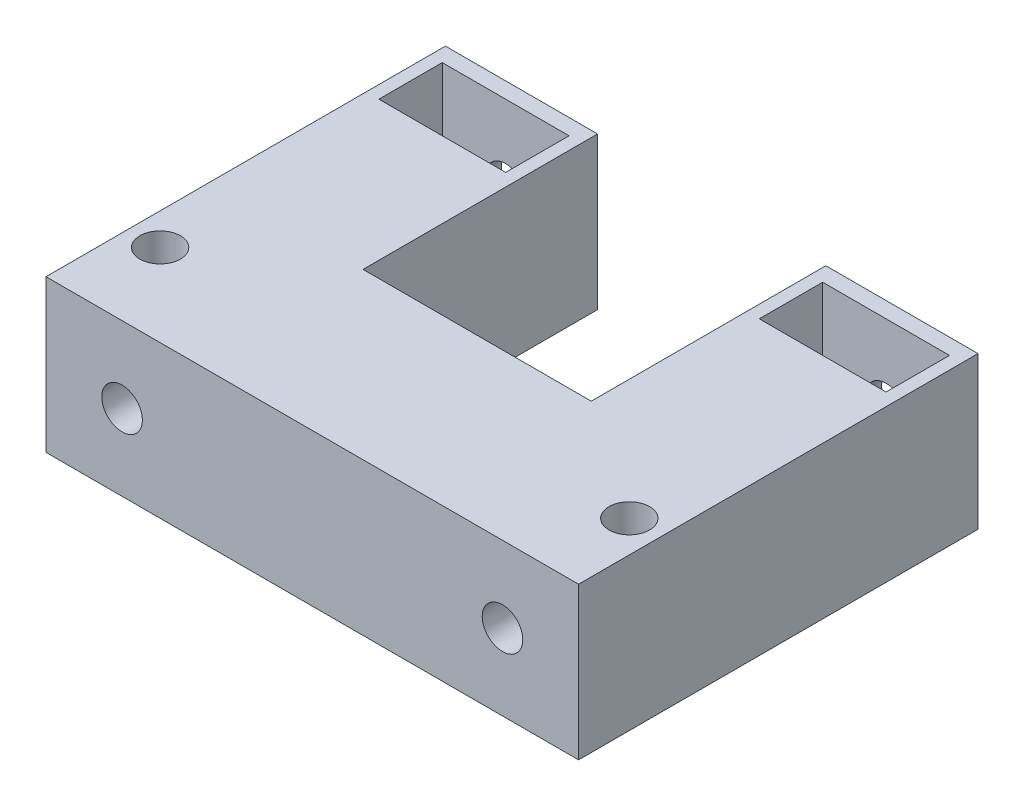
SolidWorks part; units mm, degrees
ref_plane "Alzado" through (0, 0, 0) normal (0, 0, 1) x (1, 0, 0)
ref_plane "Planta" through (0, 0, 0) normal (0, 1, 0) x (1, 0, 0)
ref_plane "Vista lateral" through (0, 0, 0) normal (1, 0, 0) x (0, 0, -1)
sketch "Croquis2" plane through (0, 0, 0) normal (0, 0, 1) x (1, 0, 0)
  line L0 (-5, -5) -> (-5, -6)
  line L1 (6, -6) -> (-6, -6)
  line L2 (6, -6) -> (6, 6)
  line L3 (6, 6) -> (-6, 6)
  line L4 (-6, -6) -> (-6, 6)
  line L7 (5, -5) -> (-5, -5)
  line L8 (5, -5) -> (5, 5)
  line L9 (5, 5) -> (-5, 5)
  line L10 (-5, -5) -> (-5, 5)
  line L14 (-5, 5) -> (-5, 6)
  line L15 (-5, 6) -> (-6, 6)
  line L16 (-6, 5) -> (-6, 6)
  line L17 (5, -5) -> (5, -6)
  line L18 (5, 5) -> (5, 6)
  point P0 (0, 0)
  point P6 (0, 0)
  dimension "D1" = 12
  dimension "D2" = 12
  dimension "D4" = 10
extrude "Saliente-Extruir1" add sketch "Croquis2" along normal blind 5 contours L10 L14 L3 L4 L1 L0 | L18 L8 L17 L1 L2 L3
sketch "Croquis3" plane through (0, 0, 0) normal (0, 0, -1) x (-1, 0, 0)
  line L0 (-6, -6) -> (-6, 6) construction
  line L1 (6, -6) -> (-6, -6)
  line L2 (6, -6) -> (6, 6)
  line L3 (6, 6) -> (-6, 6)
  line L4 (-6, -6) -> (-6, 6)
  line L5 (6, -6) -> (-6, 6) construction
  line L6 (6, 6) -> (-6, -6) construction
  point P0 (0, 0)
extrude "Saliente-Extruir2" add sketch "Croquis3" along normal blind 1.25
sketch "Croquis4" plane through (0, 0, 5) normal (0, 0, 1) x (1, 0, 0)
  line L1 (6, -6) -> (-6, -6)
  line L2 (6, -6) -> (6, 6)
  line L3 (6, 6) -> (-6, 6)
  line L4 (-6, -6) -> (-6, 6)
  line L5 (6, -6) -> (-6, 6) construction
  line L6 (6, 6) -> (-6, -6) construction
  point P0 (0, 0)
extrude "Saliente-Extruir3" add sketch "Croquis4" along normal blind 1.25
sketch "Croquis5" plane through (0, 0, 6.25) normal (0, 0, 1) x (1, 0, 0)
  circle A0 centre (0, 0) radius 1.6
extrude "Cortar-Extruir1" cut sketch "Croquis5" against normal blind 1.25
sketch "Croquis7" plane through (0, 0, 0) normal (0, 0, 1) x (1, 0, 0)
  line L1 (-6, -6) -> (6, -6)
  line L2 (-6, -6) -> (-6, 6)
  line L3 (-6, 6) -> (6, 6)
  line L4 (6, -6) -> (6, 6)
  line L5 (-6, -6) -> (6, 6) construction
  line L6 (-6, 6) -> (6, -6) construction
  circle A0 centre (0, 0) radius 1.6
sketch "Croquis9" plane through (0, 0, 0) normal (0, 0, 1) x (1, 0, 0)
  line L0 (-6, 6) -> (6, -6) construction
  circle A0 centre (0, 0) radius 1.6
extrude "Cortar-Extruir2" cut sketch "Croquis9" against normal blind 1.25
sketch "Croquis11" plane through (0, 0, 6.25) normal (0, 0, 1) x (1, 0, 0)
  line L1 (6, -6) -> (-6, -6)
  line L2 (6, -6) -> (6, 6)
  line L3 (6, 6) -> (-6, 6)
  line L4 (-6, -6) -> (-6, 6)
  line L5 (6, -6) -> (-6, 6) construction
  line L6 (6, 6) -> (-6, -6) construction
  circle A0 centre (0, 0) radius 1.6
  point P0 (0, 0)
extrude "Saliente-Extruir4" add sketch "Croquis11" along normal blind 24
sketch "Croquis12" plane through (0, 6, 0) normal (0, 1, 0) x (1, 0, 0)
  line L0 (0, 1.25) -> (0, -30.25) construction
  line L1 (-6, 1.25) -> (6, 1.25) construction
  line L2 (6, -30.25) -> (-6, -30.25) construction
  dimension "D1" = 31.5
sketch "Croquis13" plane through (6, 0, 0) normal (1, 0, 0) x (0, 0, -1)
  line L0 (-14.5, 6) -> (-14.5, -6) construction
  line L1 (1.25, 6) -> (-30.25, 6) construction
  line L2 (1.25, -6) -> (-30.25, -6) construction
  line L3 (-14.5, 0) -> (-30.25, 0) construction
  line L4 (-30.25, -6) -> (-30.25, 6) construction
  line L6 (-30.25, 6) -> (-17.25, 6)
  line L7 (-30.25, 6) -> (-30.25, -6)
  line L8 (-30.25, -6) -> (-17.25, -6)
  line L9 (-17.25, 6) -> (-17.25, -6)
  dimension "D1" = 13
extrude "Saliente-Extruir6" add sketch "Croquis13" along normal blind 30
sketch "Croquis14" plane through (0, 0, 17.25) normal (0, 0, -1) x (-1, 0, 0)
  line L0 (-36, -6) -> (-6, -6) construction
  line L1 (-36, 6) -> (-24, 6)
  line L2 (-36, 6) -> (-36, -6)
  line L3 (-36, -6) -> (-24, -6)
  line L4 (-24, 6) -> (-24, -6)
  dimension "D1" = 12
  dimension "D2" = 12
extrude "Saliente-Extruir8" add sketch "Croquis14" along normal blind 18.5
sketch "Croquis15" plane through (0, 6, 0) normal (0, 1, 0) x (1, 0, 0)
  line L0 (6, 1.25) -> (24, 1.25) construction
  line L1 (15, 1.25) -> (15, -30.25) construction
  line L2 (36, -30.25) -> (-6, -30.25) construction
  line L3 (5, 0) -> (-5, 0) construction
  line L4 (-5, 0) -> (-5, -5) construction
  line L5 (-5, -5) -> (5, -5) construction
  line L6 (5, -5) -> (5, 0) construction
  line L7 (25, 0) -> (35, 0) construction
  line L8 (35, 0) -> (35, -5) construction
  line L9 (35, -5) -> (25, -5) construction
  line L10 (25, -5) -> (25, 0) construction
  line L11 (25, 0) -> (25, -5)
  line L12 (25, -5) -> (35, -5)
  line L13 (35, -5) -> (35, 0)
  line L14 (35, 0) -> (25, 0)
extrude "Cortar-Extruir3" cut sketch "Croquis15" against normal blind 12
sketch "Croquis16" plane through (0, 0, 30.25) normal (0, 0, 1) x (1, 0, 0)
  line L0 (15, 6) -> (15, -6) construction
  line L1 (36, 6) -> (-6, 6) construction
  line L2 (-6, -6) -> (36, -6) construction
  circle A0 centre (0, 0) radius 1.6
  circle A1 centre (30, 0) radius 1.6
extrude "Cortar-Extruir5" cut sketch "Croquis16" against normal blind 32
sketch "Croquis17" plane through (0, 6, 0) normal (0, 1, 0) x (1, 0, 0)
  line L0 (6, -17.25) -> (-6, -17.25) construction
  line L1 (6, 1.25) -> (6, -17.25) construction
  line L2 (24, -17.25) -> (6, -17.25) construction
  line L3 (-6, -30.25) -> (-6, 1.25) construction
  line L4 (-6, -17.25) -> (-6, -23.75) construction
  line L5 (-6, -23.75) -> (36, -23.75) construction
  line L6 (36, 1.25) -> (36, -30.25) construction
  line L7 (15, -17.25) -> (15, -30.25) construction
  line L8 (36, -30.25) -> (-6, -30.25) construction
  circle A0 centre (-3.5, -23.75) radius 1.6
  circle A1 centre (33.5, -23.75) radius 1.6
  dimension "D3" = 37
  dimension "D1" = 13
  dimension "D2" = 6.5
  dimension "D4" = 42
extrude "Cortar-Extruir6" cut sketch "Croquis17" against normal blind 12
sketch "Croquis18" plane through (0, 0, 30.25) normal (0, 0, 1) x (1, 0, 0)
  line L0 (-1.6, 0) -> (-1.6, 6.1605) construction
  circle A0 centre (0, 0) radius 1.6 construction
sketch "Croquis20" plane through (0, 6, 0) normal (0, 1, 0) x (1, 0, 0)
  line L0 (-3.5, -23.75) -> (33.5, -23.75) construction
  dimension "D1" = 37
sketch "Croquis21" plane through (0, 0, 30.25) normal (0, 0, 1) x (1, 0, 0)
  line L0 (0, 0) -> (30, 0) construction
  dimension "D1" = 30
